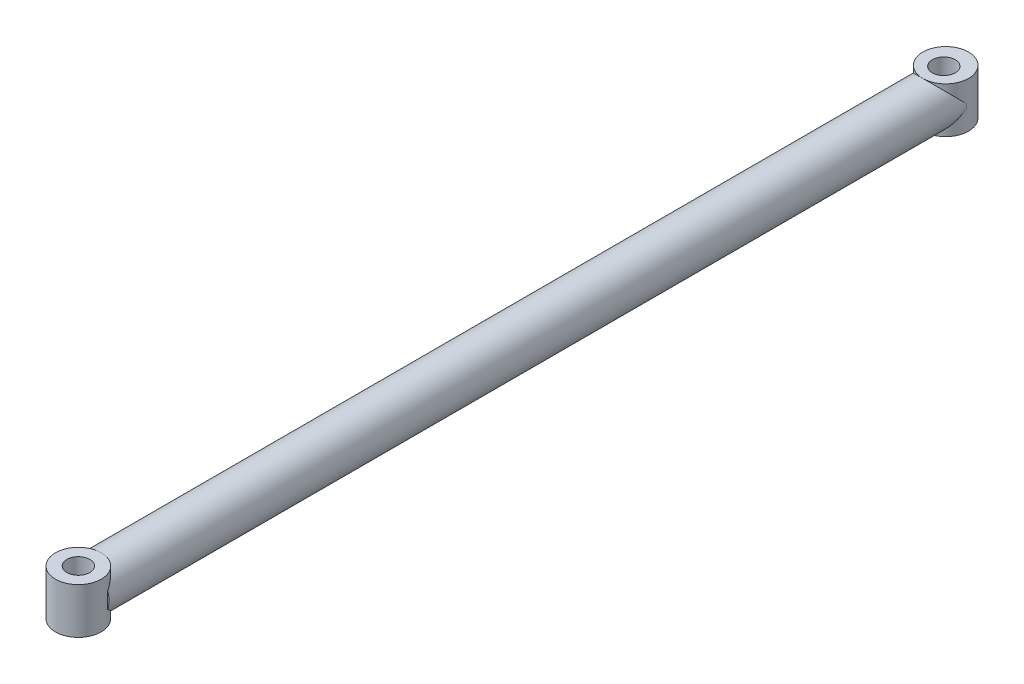
SolidWorks part; units mm, degrees
ref_plane "Ebene vorne" through (0, 0, 0) normal (0, 0, 1) x (1, 0, 0)
ref_plane "Ebene oben" through (0, 0, 0) normal (0, 1, 0) x (1, 0, 0)
ref_plane "Ebene rechts" through (0, 0, 0) normal (1, 0, 0) x (0, 0, -1)
sketch "Skizze1" plane through (0, 0, 0) normal (0, 0, 1) x (1, 0, 0)
  circle A0 centre (0, 0) radius 2
extrude "Aufsatz-Linear austragen1" add sketch "Skizze1" along normal blind 75
sketch "Skizze2" plane through (0, 0, 0) normal (0, 1, 0) x (1, 0, 0)
  circle A0 centre (0, -75.6888) radius 2
  circle A2 centre (0, 0.1611) radius 2
  point P2 (0, 1.2814)
  point P6 (0, 0.199)
  point P7 (0, 0)
  point P8 (0, -73.0224)
  point P9 (0, -75.6888)
extrude "Aufsatz-Linear austragen2" add sketch "Skizze2" against normal blind 4 from offset 2
sketch "Skizze3" plane through (0, 2, 0) normal (0, 1, 0) x (1, 0, 0)
  circle A0 centre (0, -75.6888) radius 1
  circle A1 centre (0, 0) radius 1
extrude "Schnitt-Linear austragen1" cut sketch "Skizze3" against normal blind 4
